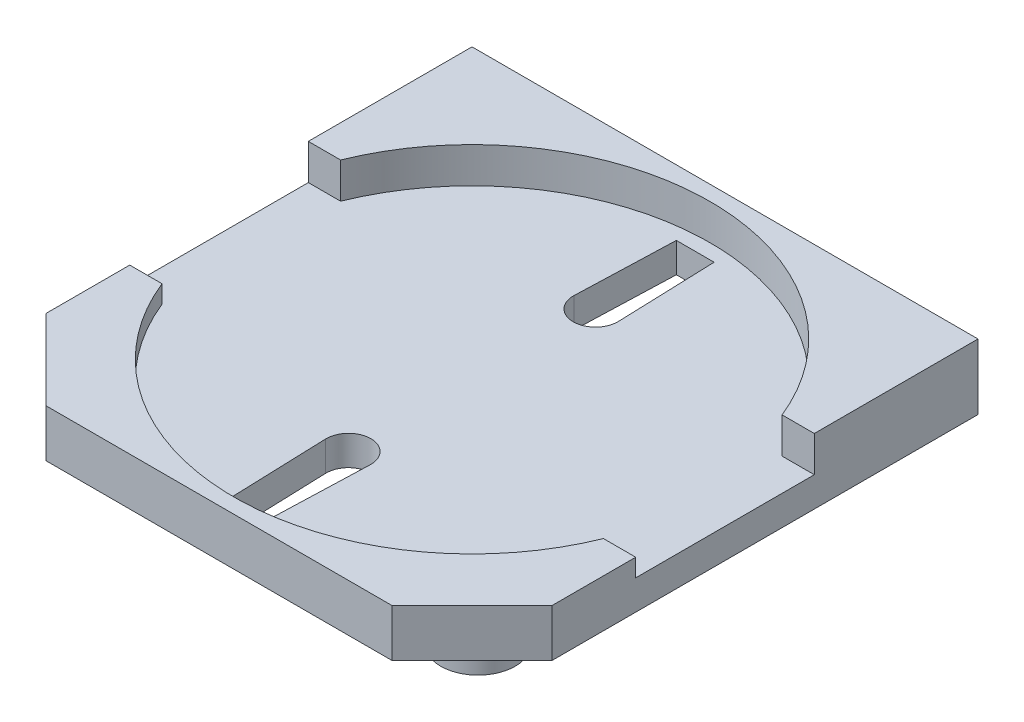
SolidWorks part; units mm, degrees
ref_plane "Front Plane" through (0, 0, 0) normal (0, 0, 1) x (1, 0, 0)
ref_plane "Top Plane" through (0, 0, 0) normal (0, 1, 0) x (1, 0, 0)
ref_plane "Right Plane" through (0, 0, 0) normal (1, 0, 0) x (0, 0, -1)
sketch "Sketch1" plane through (0, 0, 0) normal (0, 1, 0) x (1, 0, 0)
  line L1 (-8.5, -8.5) -> (8.5, -8.5)
  line L2 (-8.5, -8.5) -> (-8.5, 8.5)
  line L3 (-8.5, 8.5) -> (8.5, 8.5)
  line L4 (8.5, -8.5) -> (8.5, 8.5)
  line L5 (-8.5, -8.5) -> (8.5, 8.5) construction
  line L6 (-8.5, 8.5) -> (8.5, -8.5) construction
  point P0 (0, 0)
  dimension "D1" = 17
extrude "Boss-Extrude1" add sketch "Sketch1" along normal blind 3.5
sketch "Sketch2" plane through (0, 3.5, 0) normal (0, 1, 0) x (1, 0, 0)
  line L0 (-8.5, -5.813) -> (-5.813, -8.5)
  line L1 (-8.5, 8.5) -> (-8.5, -8.5) construction
  line L2 (-8.5, -8.5) -> (8.5, -8.5) construction
  line L3 (-5.813, -8.5) -> (-8.5, -8.5)
  line L4 (-8.5, -8.5) -> (-8.5, -5.813)
  dimension "D1" = 3.8
extrude "Cut-Extrude1" cut sketch "Sketch2" against normal through all
mirror "Mirror1" about plane through (0, 0, 0) normal (1, 0, 0) of "Cut-Extrude1"
sketch "Sketch3" plane through (0, 3.5, 0) normal (0, 1, 0) x (1, 0, 0)
  line L0 (-8.5, 3) -> (8.5, 3)
  line L1 (-8.5, 8.5) -> (-8.5, -5.813) construction
  line L2 (8.5, -5.813) -> (8.5, 8.5) construction
  line L3 (8.5, 3) -> (8.5, -5.813)
  line L4 (8.5, -5.813) -> (5.813, -8.5)
  line L5 (5.813, -8.5) -> (-5.813, -8.5)
  line L6 (-5.813, -8.5) -> (-8.5, -5.813)
  line L7 (-8.5, -5.813) -> (-8.5, 3)
  line L8 (8.5, 8.5) -> (-8.5, 8.5) construction
  dimension "D1" = 5.5
extrude "Cut-Extrude2" cut sketch "Sketch3" against normal blind 0.6
sketch "Sketch5" plane through (0, 2.9, 0) normal (0, 1, 0) x (1, 0, 0)
  line L0 (8.5, -5.813) -> (8.5, 3) construction
  line L1 (-8.5, 3) -> (8.5, 3)
  line L2 (-8.5, 3) -> (-8.5, -3)
  line L3 (-8.5, -3) -> (8.5, -3)
  line L4 (8.5, 3) -> (8.5, -3)
  line L5 (-1.925, 0) -> (1.925, 0) construction
  point P7 (-8.5, 0)
extrude "Cut-Extrude3" cut sketch "Sketch5" against normal blind 0.6
sketch "Sketch6" plane through (0, 3.5, 0) normal (0, 1, 0) x (1, 0, 0)
  circle A0 centre (0, 0) radius 8
  dimension "D1" = 16
extrude "Cut-Extrude4" cut sketch "Sketch6" against normal blind 1.2
sketch "Sketch7" plane through (0, 0, 0) normal (0, -1, 0) x (1, 0, 0)
  line L0 (0, -1.925) -> (0, 1.925) construction
  circle A0 centre (-5.5, -6.2009) radius 1.25
  circle A1 centre (-5.5, 5.2991) radius 1.25
  circle A2 centre (5.5, 5.2991) radius 1.25
  circle A3 centre (5.5, -6.2009) radius 1.25
  point P6 (0, 0)
  dimension "D1" = 2.5
  dimension "D2" = 5.5
  dimension "D3" = 11.5
extrude "Cut-Extrude5" cut sketch "Sketch7" against normal blind 1.3 flip side to cut
sketch "Sketch8" plane through (0, 1.3, 0) normal (0, -1, 0) x (1, 0, 0)
  line L0 (-0.6, -8.5) -> (0.6, -8.5)
  line L1 (-8.5, -8.5) -> (8.5, -8.5) construction
  line L2 (0, -1.925) -> (0, 1.925) construction
  line L4 (0.6, -8.5) -> (0.7496, -4.1759)
  line L5 (-0.6, -8.5) -> (-0.7496, -4.1759)
  arc A0 (0.7496, -4.1759) -> (-0.7496, -4.1759) centre (0, -4.15) ccw
  point P4 (0, -8.5)
  point P9 (0, 0)
  dimension "D2" = 1.5
  dimension "D1" = 1.2
  dimension "D3" = 4.35
extrude "Cut-Extrude6" cut sketch "Sketch8" against normal blind 1
mirror "Mirror2" about plane through (0, 0, 0) normal (0, 0, 1) of "Cut-Extrude6"
sketch "Sketch11" plane through (0, 1.3, 0) normal (0, -1, 0) x (1, 0, 0)
  line L0 (-0.6, -8.5) -> (0.6, -8.5)
  line L1 (0.6, -8.5) -> (0.6346, -7.5)
  line L2 (0.6, -8.5) -> (0.7496, -4.1759) construction
  line L3 (0.6346, -7.5) -> (-0.6346, -7.5)
  line L4 (-0.7496, -4.1759) -> (-0.6, -8.5) construction
  line L5 (-0.6346, -7.5) -> (-0.6, -8.5)
  dimension "D1" = 1
extrude "Boss-Extrude4" add sketch "Sketch11" against normal blind 1
mirror "Mirror3" about plane through (0, 0, 0) normal (0, 0, 1) of "Boss-Extrude4"
